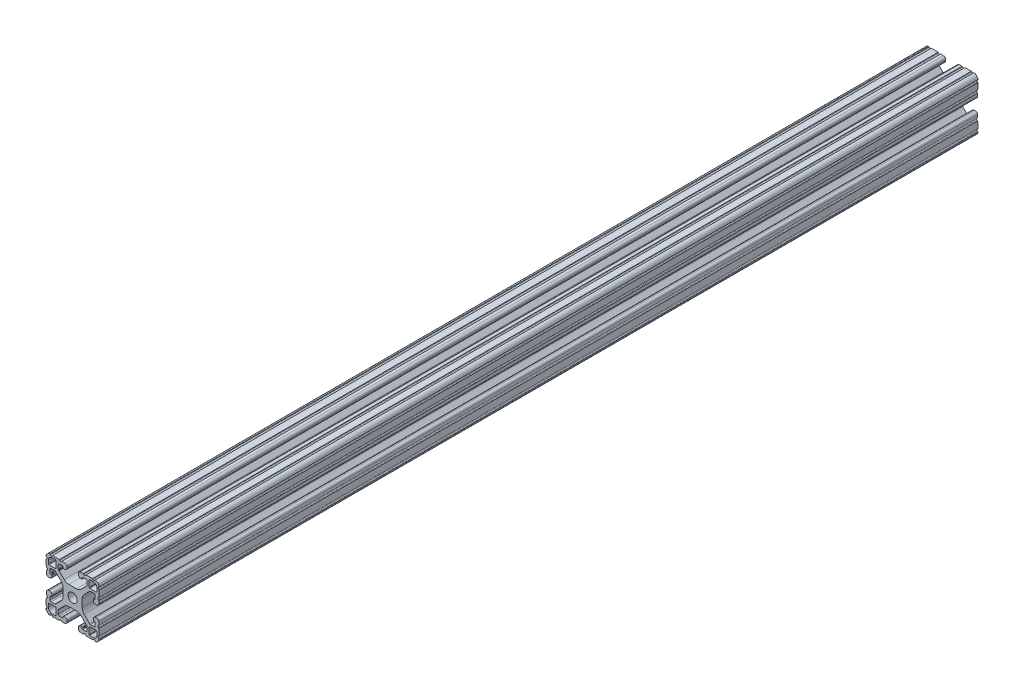
SolidWorks part; units mm, degrees
ref_plane "Front Plane" through (0, 0, 0) normal (0, 0, 1) x (1, 0, 0)
ref_plane "Top Plane" through (0, 0, 0) normal (0, 1, 0) x (1, 0, 0)
ref_plane "Right Plane" through (0, 0, 0) normal (1, 0, 0) x (0, 0, -1)
sketch "Sketch2" plane through (0, 0, 0) normal (0, 0, 1) x (1, 0, 0)
  line L0 (0, 19.05) -> (0, -19.05) construction
  line L1 (-19.05, 0) -> (19.05, 0) construction
  line L2 (4.064, -19.05) -> (19.05, -19.05) construction
  line L3 (19.05, -19.05) -> (19.05, -4.064) construction
  line L4 (4.064, -19.05) -> (4.064, -15.8768) construction
  line L5 (4.064, -15.8768) -> (13.7215, -15.8768) construction
  line L6 (13.7215, -15.8768) -> (4.7027, -6.858) construction
  line L7 (0, 0) -> (19.05, -19.05) construction
  line L8 (19.05, -4.064) -> (15.8768, -4.064) construction
  line L9 (15.8768, -4.064) -> (15.8768, -13.7215) construction
  line L10 (15.8768, -13.7215) -> (6.858, -4.7027) construction
  line L11 (11.3674, -9.2121) -> (9.2121, -11.3674) construction
  line L12 (10.287, -12.4423) -> (10.287, -15.8768) construction
  line L13 (15.7642, -19.0481) -> (4.064, -18.6395) construction
  line L14 (4.064, -18.6395) -> (4.2014, -14.7049) construction
  line L15 (4.2014, -14.7049) -> (6.858, -14.7977) construction
  line L16 (6.858, -14.7977) -> (6.858, -15.8768) construction
  line L17 (19.05, 4.064) -> (19.05, -4.064) construction
  line L18 (-19.05, -19.05) -> (19.05, -19.05) construction
  line L19 (-19.05, -19.05) -> (-19.05, 19.05) construction
  line L20 (-19.05, 19.05) -> (19.05, 19.05) construction
  line L21 (19.05, -19.05) -> (19.05, 19.05) construction
  line L22 (8.5725, -18.7969) -> (8.6004, -17.9973) construction
  line L23 (15.24, -19.0298) -> (15.2679, -18.2301) construction
  circle A0 centre (0, 0) radius 3.2639 construction
  arc A1 (18.1201, -18.1201) -> (15.7642, -19.0481) centre (15.875, -15.875) cw construction
  point P8 (0, -6.858)
  point P16 (10.2898, -10.2898)
  point P28 (11.8872, -11.8872)
  point P34 (8.5725, -18.7969)
  point P36 (15.24, -19.0298)
  point P38 (19.05, 0)
  dimension "D7" = 1.6002
  dimension "Center Hole Diameter" = 6.5278
  dimension "Corner Radius" = 3.175
  dimension "Slot Depth" = 12.192
  dimension "D1" = 3.048
  dimension "D3" = 2
  dimension "Flange Thickness" = 3.937
  dimension "D4" = 3.1732
  dimension "D2" = 20.574
  dimension "D5" = 13.716
  dimension "D6" = 7.1628
  dimension "D8" = 15.24
  dimension "D9" = 8.5725
  dimension "D10" = 0.8001
  dimension "Rail Height" = 38.1
  dimension "Rail Width" = 38.1
  dimension "T Slot Width" = 8.128
sketch "Sketch3" plane through (0, 0, 0) normal (1, 0, 0) x (0, 0, -1)
  line L0 (-457.2, 19.05) -> (457.2, 19.05) construction
  line L1 (-406.4, 0) -> (406.4, 0) construction
  dimension "Length" = 914.4
  dimension "D1" = 50.8
sketch "Sketch4" plane through (0, 0, 0) normal (0, 0, 1) x (1, 0, 0)
  line L1 (6.858, -14.7977) -> (6.858, -15.8768) construction
  line L2 (11.8872, -12.2682) -> (11.8872, -16.9436)
  line L3 (12.2549, -17.3243) -> (14.4454, -17.4008)
  line L7 (12.2682, -11.8872) -> (16.9436, -11.8872)
  line L9 (17.3243, -12.2549) -> (17.4008, -14.4454)
  line L22 (0, 0) -> (19.05, -19.05) construction
  line L23 (15.7642, -19.0481) -> (5.5961, -18.693)
  line L24 (4.064, -17.1065) -> (4.064, -16.344)
  line L25 (5.7069, -14.7575) -> (6.4903, -14.7848)
  line L26 (6.858, -15.1656) -> (6.858, -15.6891)
  line L27 (7.2257, -16.0699) -> (9.4655, -16.1481)
  line L28 (10.287, -15.3549) -> (10.287, -12.771)
  line L29 (10.0545, -12.2098) -> (6.0939, -8.2492)
  line L30 (2.7353, -6.858) -> (0, -6.858)
  line L31 (13.7215, -15.8768) -> (4.7027, -6.858) construction
  line L32 (4.064, -19.05) -> (19.05, -19.05) construction
  line L33 (4.064, -19.05) -> (4.064, -15.8768) construction
  line L34 (0, 19.05) -> (0, -19.05) construction
  line L35 (0, -3.2639) -> (0, -6.858)
  line L36 (0, 0) -> (19.1669, -19.1669) construction
  line L46 (10.287, -12.4423) -> (10.287, -15.8768) construction
  line L47 (6.858, -2.7353) -> (6.858, 0)
  line L48 (12.2098, -10.0545) -> (8.2492, -6.0939)
  line L49 (15.3549, -10.287) -> (12.771, -10.287)
  line L50 (16.0699, -7.2257) -> (16.1481, -9.4655)
  line L51 (15.1656, -6.858) -> (15.6891, -6.858)
  line L52 (14.7575, -5.7069) -> (14.7848, -6.4903)
  line L53 (17.1065, -4.064) -> (16.344, -4.064)
  line L54 (19.0481, -15.7642) -> (18.693, -5.5961)
  line L55 (3.2639, 0) -> (6.858, 0)
  arc A1 (14.4454, -17.4008) -> (17.4008, -14.4454) centre (14.5451, -14.5451) ccw
  arc A10 (16.9436, -11.8872) -> (17.3243, -12.2549) centre (16.9436, -12.2682) cw
  arc A12 (19.0481, -15.7642) -> (15.7642, -19.0481) centre (15.875, -15.875) cw
  arc A13 (3.2639, 0) -> (0, -3.2639) centre (0, 0) cw
  circle A14 centre (0, 0) radius 3.2639 construction
  arc A16 (6.0939, -8.2492) -> (2.7353, -6.858) centre (2.7353, -11.6078) ccw
  arc A17 (5.5961, -18.693) -> (4.064, -17.1065) centre (5.6515, -17.1065) cw
  arc A18 (4.064, -16.344) -> (5.7069, -14.7575) centre (5.6515, -16.344) cw
  arc A19 (9.4655, -16.1481) -> (10.287, -15.3549) centre (9.4933, -15.3549) ccw
  arc A20 (10.287, -12.771) -> (10.0545, -12.2098) centre (9.4933, -12.771) ccw
  arc A21 (6.4903, -14.7848) -> (6.858, -15.1656) centre (6.477, -15.1656) cw
  arc A22 (6.858, -15.6891) -> (7.2257, -16.0699) centre (7.239, -15.6891) ccw
  arc A23 (15.6891, -6.858) -> (16.0699, -7.2257) centre (15.6891, -7.239) cw
  arc A24 (14.7848, -6.4903) -> (15.1656, -6.858) centre (15.1656, -6.477) ccw
  arc A25 (12.771, -10.287) -> (12.2098, -10.0545) centre (12.771, -9.4933) cw
  arc A26 (16.1481, -9.4655) -> (15.3549, -10.287) centre (15.3549, -9.4933) cw
  arc A27 (16.344, -4.064) -> (14.7575, -5.7069) centre (16.344, -5.6515) ccw
  arc A28 (18.693, -5.5961) -> (17.1065, -4.064) centre (17.1065, -5.6515) ccw
  arc A29 (8.2492, -6.0939) -> (6.858, -2.7353) centre (11.6078, -2.7353) cw
  arc A30 (15.7642, -19.0481) -> (18.1201, -18.1201) centre (15.875, -15.875) ccw construction
  arc A31 (11.8872, -12.2682) -> (12.2682, -11.8872) centre (12.2682, -12.2682) cw
  arc A32 (11.8872, -16.9436) -> (12.2549, -17.3243) centre (12.2682, -16.9436) ccw
  point P33 (4.064, -18.6395)
  point P42 (6.858, -4.7027)
  point P45 (4.7027, -6.858)
  point P76 (18.6395, -4.064)
  point P89 (11.8872, -11.8872)
  dimension "D2" = 4.7498
  dimension "D3" = 0.7937
  dimension "D5" = 0.381
  dimension "D6" = 1.5875
  dimension "D8" = 2.8575
  dimension "D1" = 2
  dimension "D4" = 2.6784
  dimension "D7" = 1.6002
extrude "Boss-Extrude1" add sketch "Sketch4" along normal mid plane 914.4
sketch "Sketch8" plane through (0, 0, 0) normal (0, 0, 1) x (1, 0, 0)
  line L0 (7.6492, -18.7647) -> (9.4958, -18.8292)
  line L1 (15.7642, -19.0481) -> (4.064, -18.6395) construction
  line L2 (9.4958, -18.8292) -> (9.2789, -18.4213)
  line L3 (7.894, -18.3729) -> (7.6492, -18.7647)
  line L4 (8.5725, -18.7969) -> (8.6004, -17.9973) construction
  line L5 (14.3167, -18.9975) -> (16.1633, -19.062)
  line L7 (16.1633, -19.062) -> (15.9464, -18.6541)
  line L8 (14.5615, -18.6058) -> (14.3167, -18.9975)
  line L9 (15.24, -19.0298) -> (15.2679, -18.2301) construction
  line L10 (0, 0) -> (19.05, -19.05) construction
  line L11 (18.6058, -14.5615) -> (18.9975, -14.3167)
  line L12 (19.062, -16.1633) -> (18.6541, -15.9464)
  line L13 (18.9975, -14.3167) -> (19.062, -16.1633)
  line L14 (18.3729, -7.894) -> (18.7647, -7.6492)
  line L15 (18.8292, -9.4958) -> (18.4213, -9.2789)
  line L16 (18.7647, -7.6492) -> (18.8292, -9.4958)
  arc A0 (9.2789, -18.4213) -> (7.894, -18.3729) centre (8.5725, -18.7969) ccw
  arc A1 (15.9464, -18.6541) -> (14.5615, -18.6058) centre (15.24, -19.0298) ccw
  arc A2 (18.6541, -15.9464) -> (18.6058, -14.5615) centre (19.0298, -15.24) cw
  arc A3 (18.4213, -9.2789) -> (18.3729, -7.894) centre (18.7969, -8.5725) cw
  dimension "D1" = 60
extrude "Cut-Extrude2" cut sketch "Sketch8" against normal through all both and the other way through all
mirror "Mirror1" about plane through (0, 0, 0) normal (1, 0, 0) of bodies 142 134
mirror "Mirror2" about plane through (0, 0, 0) normal (0, 1, 0) of bodies 135
sketch "Sketch5" plane through (0, 0, 0) normal (0, 0, 1) x (1, 0, 0)
  line L0 (-6.0939, 8.2492) -> (-10.0545, 12.2098) construction
  line L1 (-10.1338, 12.508) -> (-10.1338, 12)
  line L2 (-9.9645, 11.8306) -> (-9.6506, 11.8306)
  line L3 (-9.6506, 11.8306) -> (-9.6506, 12.508)
  line L4 (-9.6506, 12.508) -> (-10.1338, 12.508)
  line L5 (-9.9046, 12.0598) -> (-9.9645, 12) construction
  circle A0 centre (-9.9046, 12.0598) radius 0.254 construction
  arc A1 (-10.287, 12.771) -> (-10.0545, 12.2098) centre (-9.4933, 12.771) ccw construction
  arc A2 (-10.1338, 12) -> (-9.9645, 11.8306) centre (-9.9645, 12) ccw
  dimension "D2" = 0.508
  dimension "D3" = 0.1693
  dimension "D1" = 0.7112
  dimension "D4" = 0.508
extrude "Cut-Extrude1" cut sketch "Sketch5" against normal through all both and the other way through all
ref_plane "Plane1" through (0, 19.05, 0) normal (0, 1, 0) x (-1, 0, 0)
ref_plane "Plane2" through (19.05, 0, 0) normal (1, 0, 0) x (0, 0, -1)
ref_plane "Plane3" through (0, -19.05, 0) normal (0, -1, 0) x (1, 0, 0)
ref_plane "Plane4" through (-19.05, 0, 0) normal (-1, 0, 0) x (0, 0, 1)
sketch "Sketch10" plane through (0, 0, 0) normal (1, 0, 0) x (0, 0, -1)
  line L0 (457.2, 14.3167) -> (457.2, 9.4958) construction
  line L1 (-504.4866, 46.4178) -> (-171.25, 46.4178)
  line L2 (-504.4866, 46.4178) -> (-504.4866, -36.7876)
  line L3 (-504.4866, -36.7876) -> (-171.25, -36.7876)
  line L4 (-171.25, 46.4178) -> (-171.25, -36.7876)
  point P6 (-504.2666, 46.4178)
  dimension "D1" = 628.45
extrude "Cut-Extrude5" cut sketch "Sketch10" against normal mid plane 58.42
equation "\"D1@Boss-Extrude1\"=\"Length@Sketch3\""
equation "\"D6@Sketch4\"=\"Corner Radius@Sketch2\"/2"
equation "\"D3@Sketch4\"=\"D6@Sketch4\"/2"
equation "\"D4@Sketch2\"=\"Flange Thickness@Sketch2\"*.806"
equation "\"D7@Sketch4\"=\"D7@Sketch2\""
equation "\"D8@Sketch4\"=\"Corner Radius@Sketch2\"*.9"
equation "\"D3@Sketch5\"=\"D2@Sketch5\"/3"
equation "\"D4@Sketch5\"=\"D2@Sketch5\""
equation "\"D8@Sketch2\"=\"Rail Width@Sketch2\"*.4"
equation "\"D9@Sketch2\"=\"Rail Width@Sketch2\"*.225"
equation "\"D10@Sketch2\"=\"D7@Sketch2\"/2"
